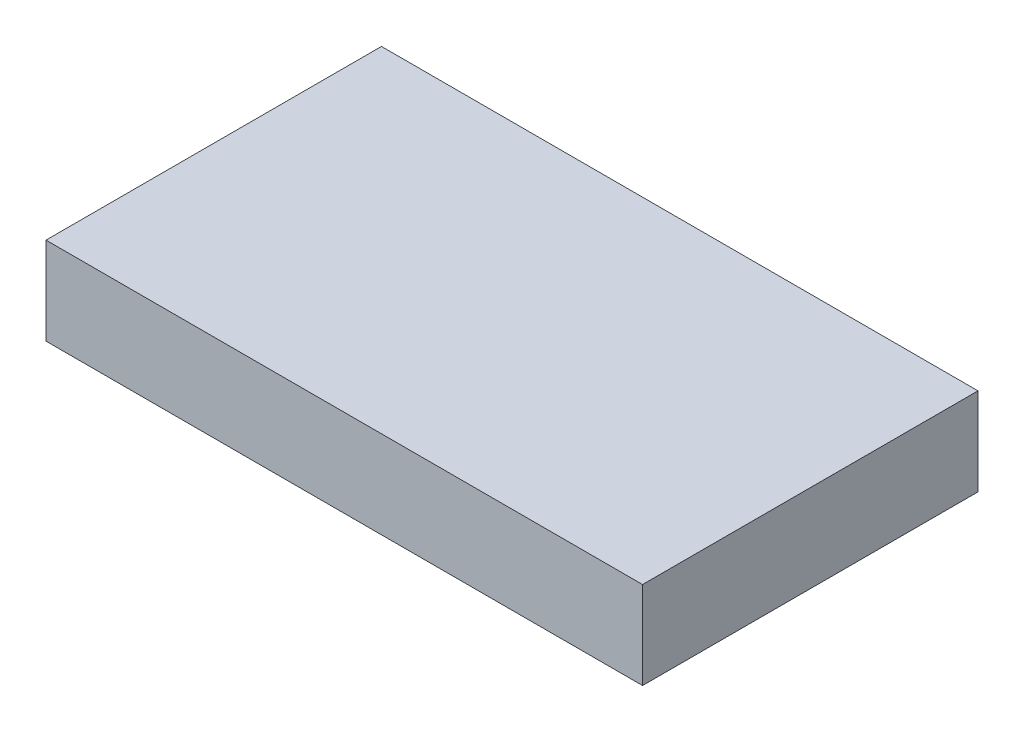
SolidWorks part; units mm, degrees
ref_plane "Front Plane" through (0, 0, 0) normal (0, 0, 1) x (1, 0, 0)
ref_plane "Top Plane" through (0, 0, 0) normal (0, 1, 0) x (1, 0, 0)
ref_plane "Right Plane" through (0, 0, 0) normal (1, 0, 0) x (0, 0, -1)
sketch "Sketch1" plane through (0, 0, 0) normal (0, 1, 0) x (1, 0, 0)
  line L1 (-71.3652, 52.8464) -> (32.5208, 52.8464)
  line L2 (-71.3652, 52.8464) -> (-71.3652, -5.5736)
  line L3 (-71.3652, -5.5736) -> (32.5208, -5.5736)
  line L4 (32.5208, 52.8464) -> (32.5208, -5.5736)
  dimension "D1" = 103.886
  dimension "D2" = 58.42
extrude "Boss-Extrude1" add sketch "Sketch1" along normal blind 15.24
